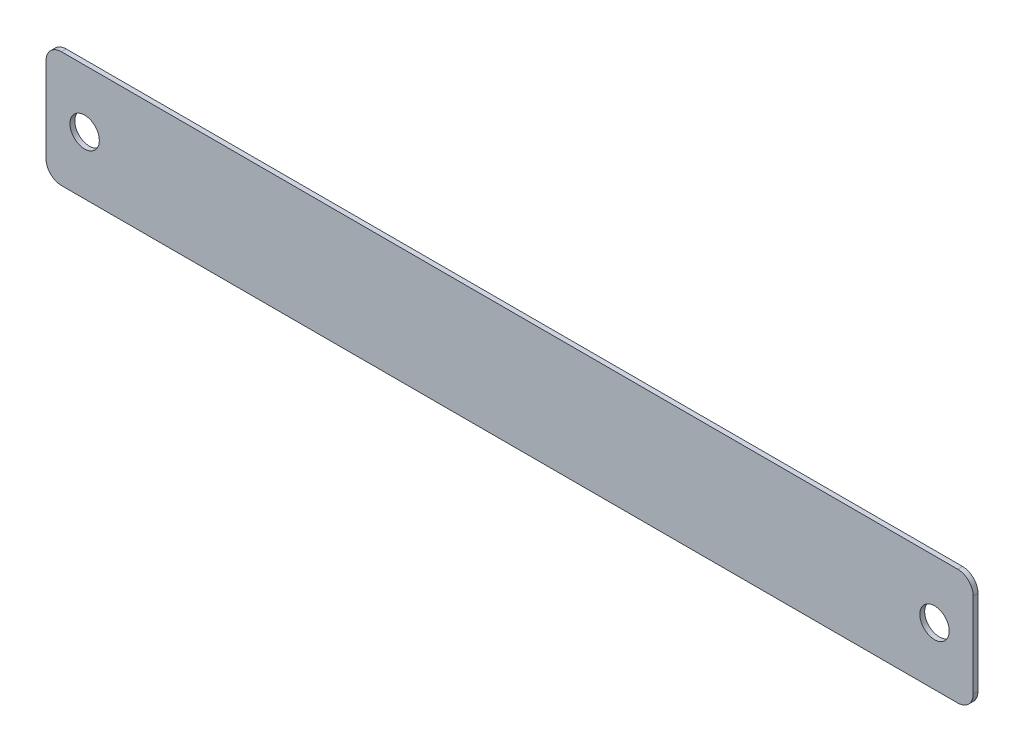
SolidWorks part; units mm, degrees
material "6061-T6 (SS)"
ref_plane "Front Plane" through (0, 0, 0) normal (0, 0, 1) x (1, 0, 0)
ref_plane "Top Plane" through (0, 0, 0) normal (0, 1, 0) x (1, 0, 0)
ref_plane "Right Plane" through (0, 0, 0) normal (1, 0, 0) x (0, 0, -1)
sketch "Sketch1" plane through (0, 0, 0) normal (0, 0, 1) x (1, 0, 0)
  line L1 (0, 0) -> (152.4, 0)
  line L2 (0, 0) -> (0, 19.05)
  line L3 (0, 19.05) -> (152.4, 19.05)
  line L4 (152.4, 0) -> (152.4, 19.05)
  circle A0 centre (6.35, 9.525) radius 2.413
  circle A1 centre (146.05, 9.525) radius 2.413
  dimension "D3" = 4.826
  dimension "D4" = 4.826
  dimension "D5" = 6.35
  dimension "D6" = 6.35
  dimension "D7" = 9.525
  dimension "D8" = 9.525
  dimension "D1" = 19.05
  dimension "D2" = 152.4
extrude "Boss-Extrude1" add sketch "Sketch1" along normal blind 0.7937
fillet "Fillet1" radius 2.54 4 edges at (0, 19.05, 0.3969) (152.4, 0, 0.3969) (0, 0, 0.3969) (152.4, 19.05, 0.3969)
